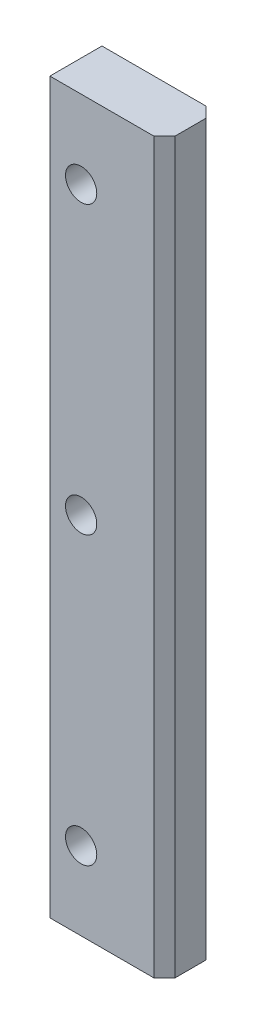
SolidWorks part; units mm, degrees
material "PA Type 6"
ref_plane "Front Plane" through (0, 0, 0) normal (0, 0, 1) x (1, 0, 0)
ref_plane "Top Plane" through (0, 0, 0) normal (0, 1, 0) x (1, 0, 0)
ref_plane "Right Plane" through (0, 0, 0) normal (1, 0, 0) x (0, 0, -1)
sketch "Sketch1" plane through (0, 0, 0) normal (0, 0, 1) x (1, 0, 0)
  line L0 (-11, -70) -> (-11, 70)
  line L1 (-11, 70) -> (11, 70)
  line L2 (11, 70) -> (11, -70)
  line L3 (11, -70) -> (-11, -70)
  line L4 (-82.3128, 0) -> (146.2829, 0) construction
  line L5 (0, 330.0605) -> (0, -326.1743) construction
  dimension "D1" = 22
  dimension "D2" = 140
extrude "Boss-Extrude1" add sketch "Sketch1" along normal blind 10
chamfer "Chamfer1" distance 2 angle 45 2 edges at (11, 0, 10) (11, 0, 0)
sketch "Sketch2" plane through (0, 0, 10) normal (0, 0, 1) x (1, 0, 0)
  line L0 (-39.0755, 0) -> (76.2606, 0) construction
  line L2 (-5, 181.9915) -> (-5, -71.9915) construction
  line L3 (-11, 70) -> (-11, -70) construction
  circle A0 centre (-5, 55) radius 3
  circle A1 centre (-5, 0) radius 3
  circle A2 centre (-5, -55) radius 3
  dimension "D3" = 6
  dimension "D1" = 110
  dimension "D2" = 6
extrude "Cut-Extrude1" cut sketch "Sketch2" against normal through all
